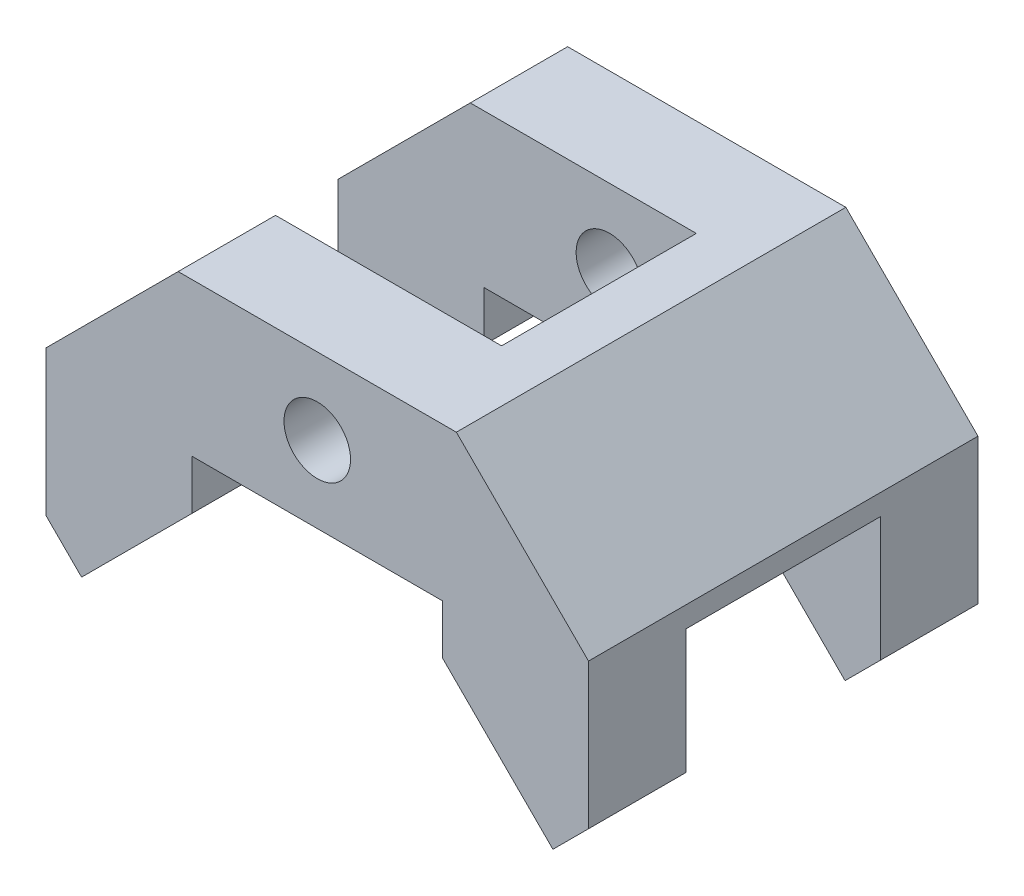
SolidWorks part; units mm, degrees
ref_plane "前视基准面" through (0, 0, 0) normal (0, 0, 1) x (1, 0, 0)
ref_plane "上视基准面" through (0, 0, 0) normal (0, 1, 0) x (1, 0, 0)
ref_plane "右视基准面" through (0, 0, 0) normal (1, 0, 0) x (0, 0, -1)
other "Configuration Table"
sketch "草图1" plane through (0, 0, 0) normal (0, 0, 1) x (1, 0, 0)
  line L0 (0, 0) -> (0, -32.3426) construction
  line L1 (0, 0) -> (-20, 0)
  line L2 (-20, 0) -> (-39, -19)
  line L3 (-39, -19) -> (-39, -39.8823)
  line L4 (-39, -39.8823) -> (-33.8848, -44.9975)
  line L5 (-33.8848, -44.9975) -> (-18, -29.1127)
  line L6 (-18, -29.1127) -> (-18, -22)
  line L7 (-18, -22) -> (18, -22)
  line L8 (18, -22) -> (18, -29.1127)
  line L9 (18, -29.1127) -> (33.8848, -44.9975)
  line L10 (33.8848, -44.9975) -> (39, -39.8823)
  line L11 (39, -39.8823) -> (39, -19)
  line L12 (39, -19) -> (20, 0)
  line L13 (20, 0) -> (0, 0)
  circle A0 centre (0, -11) radius 4.7815
  dimension "D12" = 11
  dimension "D1" = 20
  dimension "D2" = 20
  dimension "D3" = 39
  dimension "D4" = 39
  dimension "D5" = 45
  dimension "D6" = 45
  dimension "D7" = 18
  dimension "D8" = 18
  dimension "D9" = 22
  dimension "D10" = 22
  dimension "D11" = 22
  dimension "D13" = 48
  dimension "D14" = 48
extrude "凸台-拉伸1" add sketch "草图1" along normal mid plane 56
sketch "草图2" plane through (0, 0, 0) normal (0, 1, 0) x (1, 0, 0)
  line L0 (0, 0) -> (-50.0274, 0) construction
  line L1 (-39, 14) -> (12.5, 14)
  line L2 (-39, -28) -> (-39, 28) construction
  line L3 (12.5, 14) -> (12.5, -14)
  line L4 (12.5, 0) -> (-39, 0) construction
  line L5 (-39, -14) -> (-39, 14)
  line L6 (-39, -14) -> (12.5, -14)
  dimension "D1" = 14
  dimension "D2" = 12.5
extrude "切除-拉伸1" cut sketch "草图2" against normal through all
sketch "草图3" plane through (12.5, 0, 0) normal (-1, 0, 0) x (0, 0, 1)
  line L0 (-14, -22) -> (14, -22)
  line L1 (14, -22) -> (14, -45.2358)
  line L2 (14, -45.2358) -> (-14, -45.2358)
  line L3 (-14, -45.2358) -> (-14, -22)
extrude "切除-拉伸2" cut sketch "草图3" against normal through all
sketch "草图4" plane through (-39.4411, -39.4411, 0) normal (-0.7071, -0.7071, 0) x (0, 0, 1)
  line L0 (-28.5, -7.8579) -> (-26, -5.3579)
  line L1 (-14, -7.8579) -> (-28, -7.8579) construction
  line L2 (-21, -5.3579) -> (-21, 6.2862) construction
  line L3 (-26, -5.3579) -> (-23.5, -7.8579)
  line L4 (-23.5, -7.8579) -> (-21, -5.3579)
  line L5 (-21, -5.3579) -> (-18.5, -7.8579)
  line L6 (-28, -2.8284) -> (-28, -28.2843) construction
  line L7 (-13.5, -7.8579) -> (-16, -5.3579)
  line L8 (-16, -5.3579) -> (-18.5, -7.8579)
  dimension "D1" = 45
  dimension "D2" = 45
  dimension "D3" = 2
  dimension "D5" = 5
  dimension "D6" = 5
